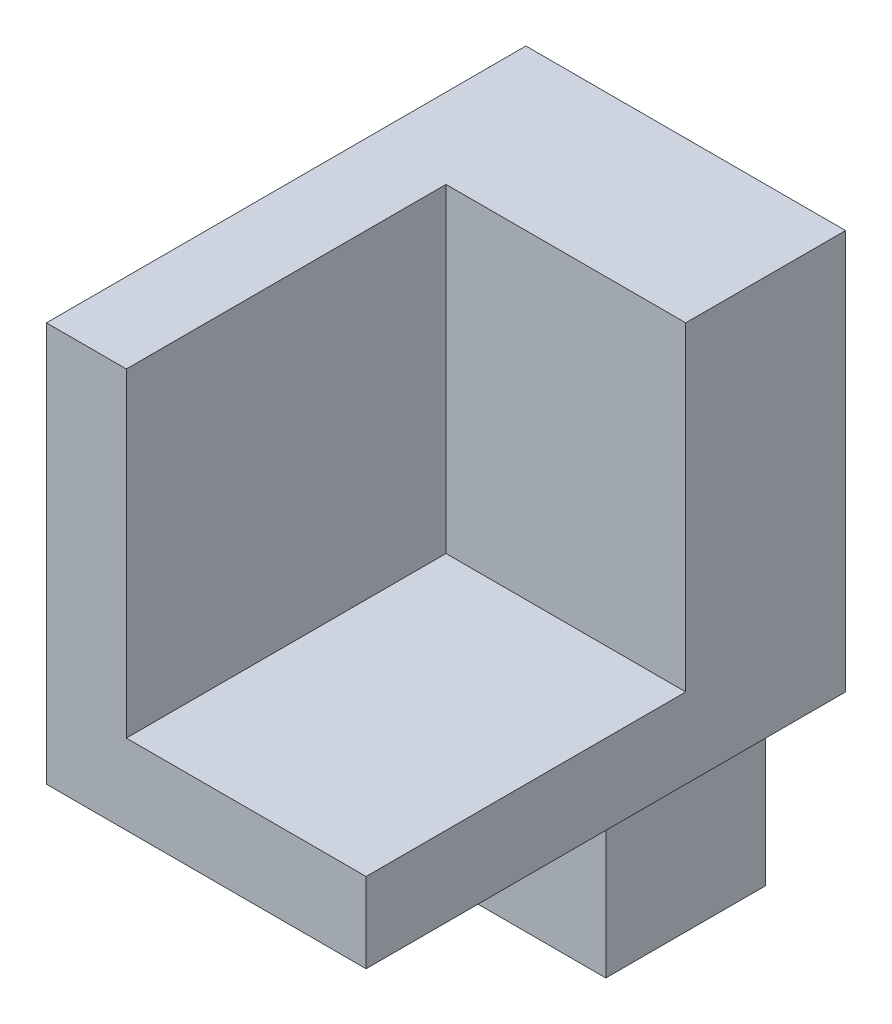
SolidWorks part; units mm, degrees
ref_plane "Front Plane" through (0, 0, 0) normal (0, 0, 1) x (1, 0, 0)
ref_plane "Top Plane" through (0, 0, 0) normal (0, 1, 0) x (1, 0, 0)
ref_plane "Right Plane" through (0, 0, 0) normal (1, 0, 0) x (0, 0, -1)
sketch "Sketch1" plane through (0, 0, 0) normal (1, 0, 0) x (0, 0, -1)
  line L0 (0, -1509.5556) -> (0, 73968.222) construction
  line L1 (0, 0) -> (-10, 0)
  line L2 (-10, 0) -> (-10, -20)
  line L3 (-10, -20) -> (-30, -20)
  line L6 (0, -38) -> (0, 0)
  line L7 (-30, -20) -> (-30, -25)
  line L8 (-30, -25) -> (-10, -25)
  line L9 (-10, -25) -> (-10, -38)
  line L10 (-10, -38) -> (0, -38)
  dimension "D1" = 20
  dimension "D2" = 20
  dimension "D3" = 5
  dimension "D4" = 10
  dimension "D5" = 10
  dimension "D6" = 38
extrude "Boss-Extrude1" add sketch "Sketch1" along normal blind 10
sketch "Sketch2" plane through (0, 0, 0) normal (-1, 0, 0) x (0, 0, 1)
  line L1 (0, 0) -> (30, 0)
  line L2 (0, 0) -> (0, -25)
  line L3 (0, -25) -> (30, -25)
  line L4 (30, 0) -> (30, -25)
extrude "Boss-Extrude2" add sketch "Sketch2" along normal blind 5
sketch "Sketch3" plane through (10, 0, 0) normal (1, 0, 0) x (0, 0, -1)
  line L0 (-10, 0) -> (-10, -20)
  line L1 (-10, -20) -> (-30, -20)
  line L2 (-30, -20) -> (-30, -25)
  line L3 (-30, -25) -> (-10, -25)
  line L4 (-10, -25) -> (0, -25)
  line L5 (0, -25) -> (0, 0)
  line L6 (0, 0) -> (-10, 0)
extrude "Boss-Extrude3" add sketch "Sketch3" along normal blind 5
